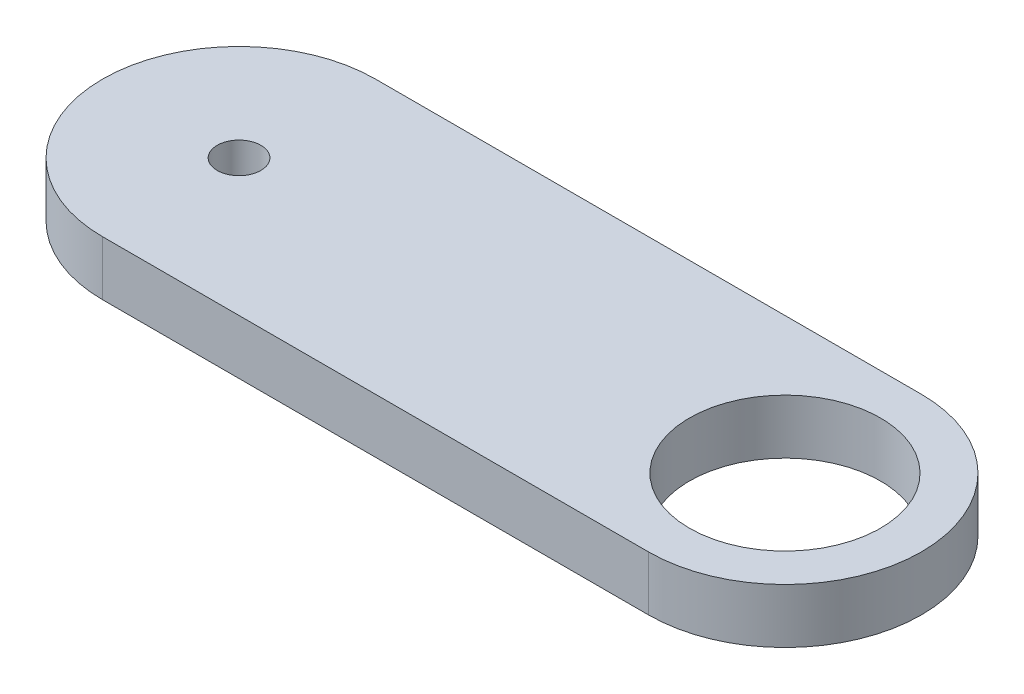
SolidWorks part; units mm, degrees
ref_plane "Front Plane" through (0, 0, 0) normal (0, 0, 1) x (1, 0, 0)
ref_plane "Top Plane" through (0, 0, 0) normal (0, 1, 0) x (1, 0, 0)
ref_plane "Right Plane" through (0, 0, 0) normal (1, 0, 0) x (0, 0, -1)
sketch "Sketch1" plane through (0, 0, 0) normal (0, 1, 0) x (1, 0, 0)
  line L0 (0, 0) -> (100, 0) construction
  line L2 (0, 25) -> (100, 25)
  line L3 (0, -25) -> (100, -25)
  arc A0 (0, 25) -> (0, -25) centre (0, 0) ccw
  arc A1 (100, -25) -> (100, 25) centre (100, 0) ccw
  circle A2 centre (0, 0) radius 4
  circle A8 centre (100, 0) radius 17.5
  point P5 (50, 0)
  dimension "D1" = 25
  dimension "D3" = 8
  dimension "D7" = 35
extrude "Boss-Extrude1" add sketch "Sketch1" along normal blind 10
